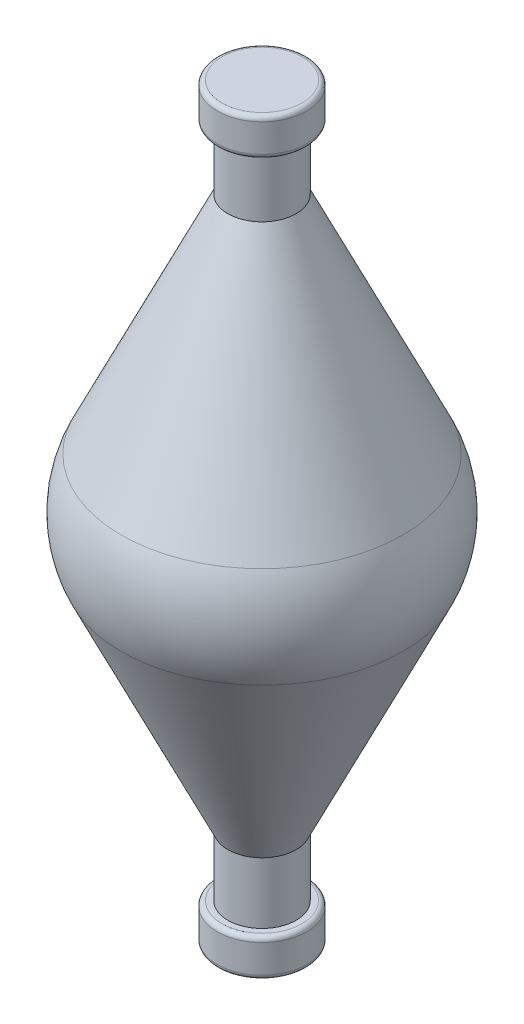
SolidWorks part; units mm, degrees
ref_plane "Plan de face" through (0, 0, 0) normal (0, 0, 1) x (1, 0, 0)
ref_plane "Plan de dessus" through (0, 0, 0) normal (0, 1, 0) x (1, 0, 0)
ref_plane "Plan de droite" through (0, 0, 0) normal (1, 0, 0) x (0, 0, -1)
sketch "Esquisse1" plane through (0, 0, 0) normal (0, 0, 1) x (1, 0, 0)
  line L0 (0, 15.9) -> (0, -15.9)
  line L1 (0, 15.9) -> (1.9, 15.9)
  line L2 (1.9, 15.9) -> (1.9, 14.3)
  line L3 (1.9, 14.3) -> (1.45, 14.3)
  line L4 (1.45, 14.3) -> (1.45, 11.7)
  line L5 (1.45, 11.7) -> (7, 0)
  line L6 (7, 0) -> (1.45, -11.7)
  line L7 (1.45, -11.7) -> (1.45, -14.3)
  line L8 (1.45, -14.3) -> (1.9, -14.3)
  line L9 (1.9, -14.3) -> (1.9, -15.9)
  line L10 (1.9, -15.9) -> (0, -15.9)
  point P3 (0, 0)
  dimension "D1" = 1.6
  dimension "D2" = 1.9
  dimension "D3" = 1.45
  dimension "D4" = 7
  dimension "D5" = 2.6
  dimension "D6" = 28.6
revolve "Révolution1" add sketch "Esquisse1" angle 360 about L0
fillet "Congé1" radius 5 1 edges at (-7, 0, 0)
fillet "Congé2" radius 0.2 4 edges at (-1.9, 15.9, 0) (-1.9, 14.3, 0) (-1.9, -15.9, 0) (-1.9, -14.3, 0)
